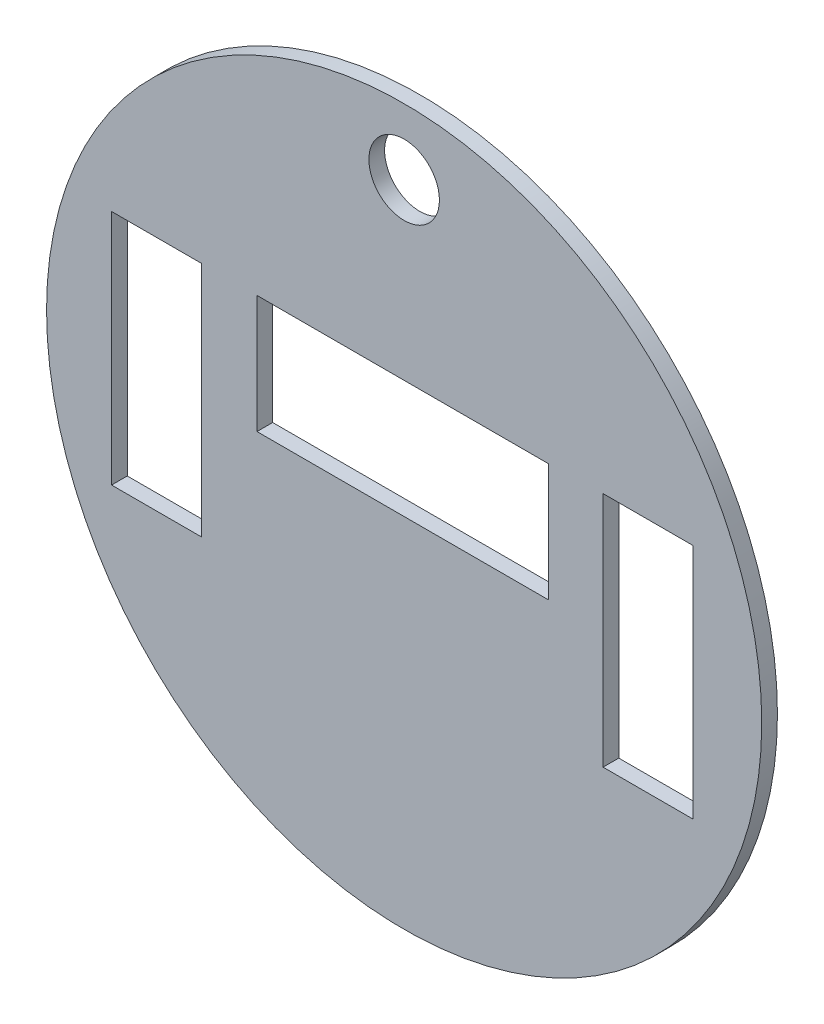
SolidWorks part; units mm, degrees
ref_plane "Front Plane" through (0, 0, 0) normal (0, 0, 1) x (1, 0, 0)
ref_plane "Top Plane" through (0, 0, 0) normal (0, 1, 0) x (1, 0, 0)
ref_plane "Right Plane" through (0, 0, 0) normal (1, 0, 0) x (0, 0, -1)
sketch "Sketch1" plane through (0, 0, 0) normal (0, 0, 1) x (1, 0, 0)
  line L0 (173.8271, 104.2809) -> (252.6073, 104.2809)
  line L1 (-255.668, 103.0316) -> (-176.8879, 103.0316)
  line L2 (-255.668, 103.0316) -> (-255.668, -104.0018)
  line L3 (-255.668, -104.0018) -> (-176.8879, -104.0018)
  line L4 (-176.8879, 103.0316) -> (-176.8879, -104.0018)
  line L5 (173.8271, 104.2809) -> (173.8271, -102.7525)
  line L6 (173.8271, -102.7525) -> (252.6073, -102.7525)
  line L7 (252.6073, 104.2809) -> (252.6073, -102.7525)
  line L9 (-128.6066, 103.0316) -> (126.1813, 103.0316)
  line L10 (-128.6066, 103.0316) -> (-128.6066, 0)
  line L11 (-128.6066, 0) -> (126.1813, 0)
  line L12 (126.1813, 103.0316) -> (126.1813, 0)
  circle A0 centre (0, 0) radius 312.4978
  circle A1 centre (0, 254.8435) radius 30.8151
extrude "Boss-Extrude1" add sketch "Sketch1" along normal blind 13.716
